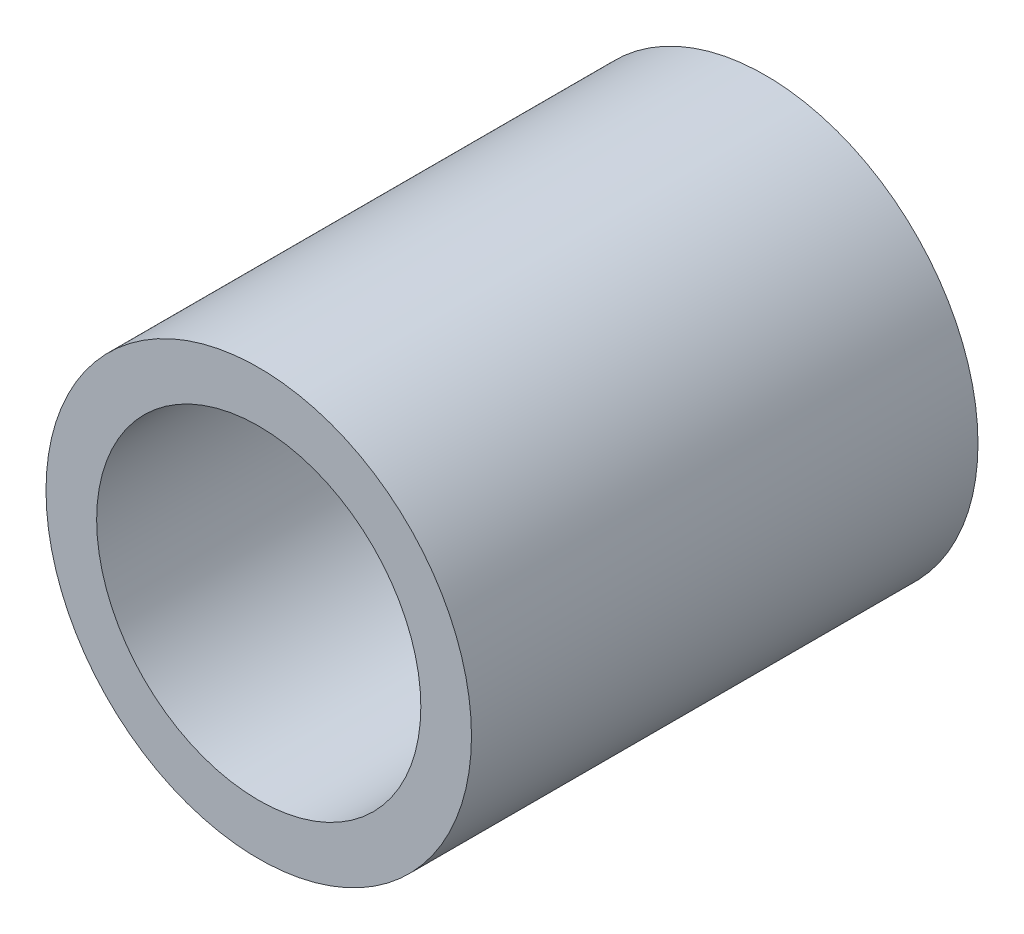
SolidWorks part; units mm, degrees
material "AISI 304"
ref_plane "正面" through (0, 0, 0) normal (0, 0, 1) x (1, 0, 0)
ref_plane "平面" through (0, 0, 0) normal (0, 1, 0) x (1, 0, 0)
ref_plane "右側面" through (0, 0, 0) normal (1, 0, 0) x (0, 0, -1)
sketch "Sketch1" plane through (0, 0, 0) normal (0, 0, 1) x (1, 0, 0)
  circle A0 centre (0, 0) radius 2.1
extrude "Boss-Extrude1" add sketch "Sketch1" along normal blind 5
shell "Shell1" thickness 0.5
